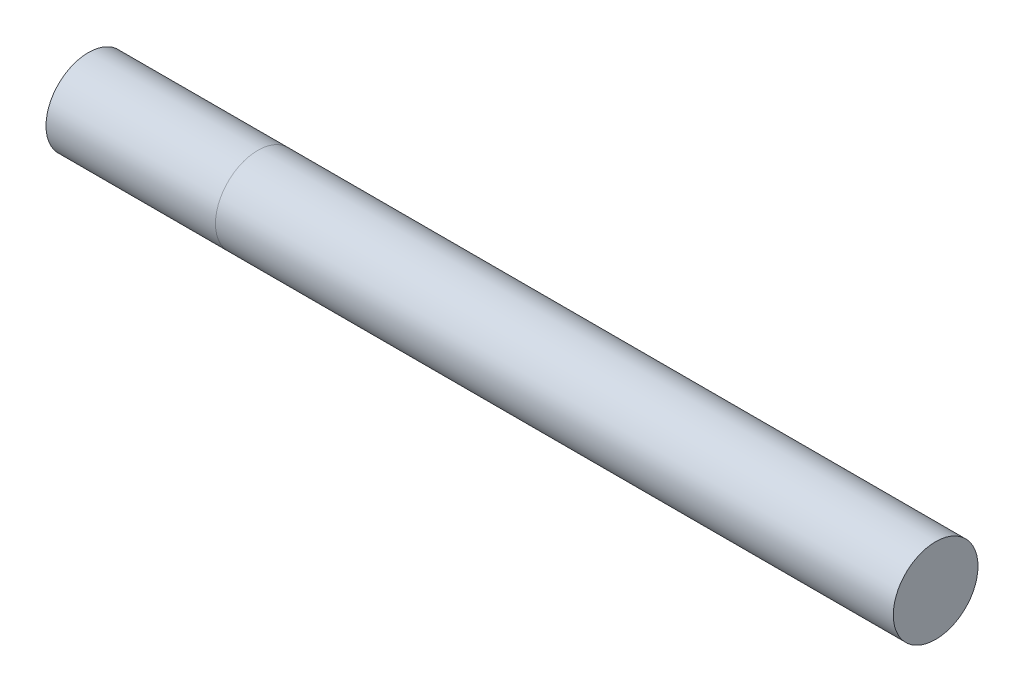
SolidWorks part; units mm, degrees
ref_plane "Front Plane" through (0, 0, 0) normal (0, 0, 1) x (1, 0, 0)
ref_plane "Top Plane" through (0, 0, 0) normal (0, 1, 0) x (1, 0, 0)
ref_plane "Right Plane" through (0, 0, 0) normal (1, 0, 0) x (0, 0, -1)
sketch "Sketch1" plane through (0, 0, 0) normal (1, 0, 0) x (0, 0, -1)
  circle A0 centre (0, 0) radius 12.5
  dimension "D1" = 25
extrude "Boss-Extrude1" add sketch "Sketch1" along normal blind 250
ref_plane "Plane1" through (50, 0, 0) normal (-1, 0, 0) x (0, 0, 1)
split line "Split Line1"
